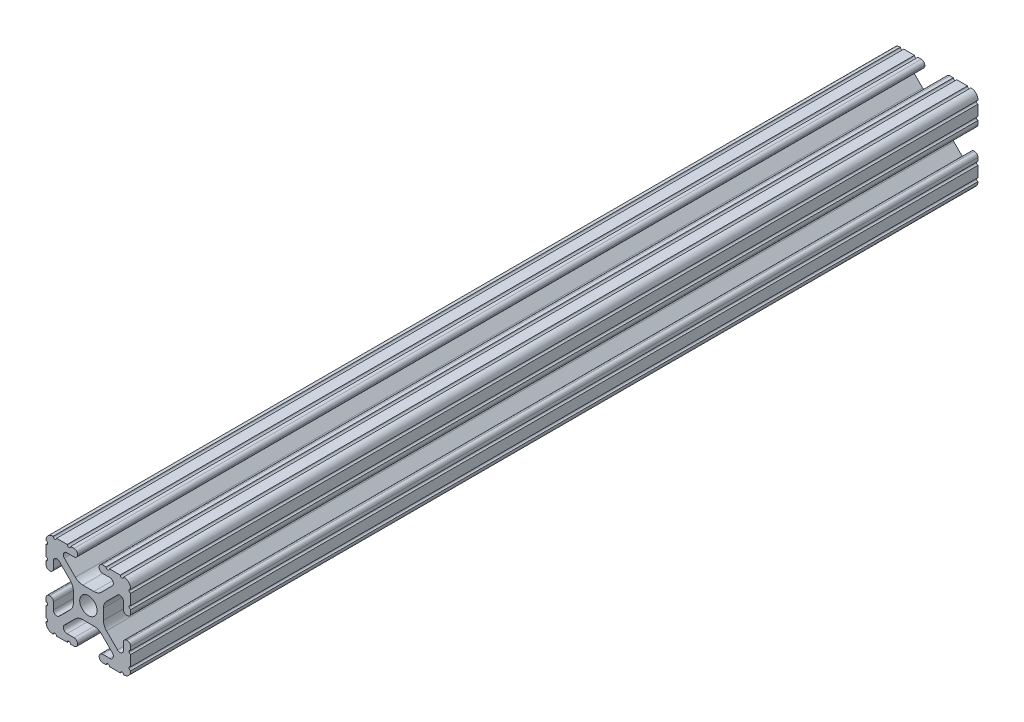
SolidWorks part; units mm, degrees
ref_plane "Front" through (0, 0, 0) normal (0, 0, 1) x (1, 0, 0)
ref_plane "Top" through (0, 0, 0) normal (0, 1, 0) x (1, 0, 0)
ref_plane "Right" through (0, 0, 0) normal (1, 0, 0) x (0, 0, -1)
sketch "Sketch1" plane through (0, 0, 0) normal (0, 0, 1) x (1, 0, 0)
  line L0 (-7.5107, 9.4563) -> (7.5107, 9.4563) construction
  line L1 (-7.4968, -9.4098) -> (7.4968, -9.4098) construction
  line L88 (-7.1797, -8.6452) -> (-3.9523, -5.4237)
  line L89 (-1.7093, -4.4958) -> (1.7093, -4.4958)
  line L90 (3.9523, -5.4237) -> (7.1797, -8.6452)
  line L91 (6.4164, -10.4902) -> (4.2875, -10.4902)
  line L92 (3.2385, -11.5392) -> (3.2385, -11.651)
  line L93 (4.2875, -12.7) -> (5.3171, -12.7)
  line L94 (6.3331, -12.7) -> (9.5504, -12.7)
  line L95 (12.7, -9.5504) -> (12.7, -6.3331)
  line L96 (12.7, -5.3171) -> (12.7, -4.2875)
  line L97 (11.651, -3.2385) -> (11.5392, -3.2385)
  line L98 (10.4902, -4.2875) -> (10.4902, -6.4021)
  line L99 (8.7371, -7.1294) -> (5.441, -3.8408)
  line L100 (4.5085, -1.5932) -> (4.5085, 1.5932)
  line L101 (5.441, 3.8408) -> (8.7371, 7.1294)
  line L102 (10.4902, 6.4021) -> (10.4902, 4.2875)
  line L103 (11.5392, 3.2385) -> (11.651, 3.2385)
  line L104 (12.7, 4.2875) -> (12.7, 5.3171)
  line L105 (12.7, 6.3331) -> (12.7, 9.5504)
  line L106 (9.5504, 12.7) -> (6.3331, 12.7)
  line L107 (5.3171, 12.7) -> (4.2875, 12.7)
  line L108 (3.2385, 11.651) -> (3.2385, 11.5392)
  line L109 (4.2875, 10.4902) -> (6.4768, 10.4902)
  line L110 (7.207, 8.7244) -> (3.8983, 5.4232)
  line L111 (1.6558, 4.4958) -> (-1.6558, 4.4958)
  line L112 (-3.8983, 5.4232) -> (-7.207, 8.7244)
  line L113 (-6.4768, 10.4902) -> (-4.2875, 10.4902)
  line L114 (-3.2385, 11.5392) -> (-3.2385, 11.651)
  line L115 (-4.2875, 12.7) -> (-5.3171, 12.7)
  line L116 (-6.3331, 12.7) -> (-9.5504, 12.7)
  line L117 (-12.7, 9.5504) -> (-12.7, 6.3331)
  line L118 (-12.7, 5.3171) -> (-12.7, 4.2875)
  line L119 (-11.651, 3.2385) -> (-11.5392, 3.2385)
  line L120 (-10.4902, 4.2875) -> (-10.4902, 6.4021)
  line L121 (-8.7371, 7.1294) -> (-5.441, 3.8408)
  line L122 (-4.5085, 1.5932) -> (-4.5085, -1.5932)
  line L123 (-5.441, -3.8408) -> (-8.7371, -7.1294)
  line L124 (-10.4902, -6.4021) -> (-10.4902, -4.2875)
  line L125 (-11.5392, -3.2385) -> (-11.651, -3.2385)
  line L126 (-12.7, -4.2875) -> (-12.7, -5.3171)
  line L127 (-12.7, -6.3331) -> (-12.7, -9.5504)
  line L128 (-9.5504, -12.7) -> (-6.3331, -12.7)
  line L129 (-5.3171, -12.7) -> (-4.2875, -12.7)
  line L130 (-3.2385, -11.651) -> (-3.2385, -11.5392)
  line L131 (-4.2875, -10.4902) -> (-6.4164, -10.4902)
  circle A1 centre (0, 0) radius 2.6035
  arc A104 (-7.1797, -8.6452) -> (-6.4164, -10.4902) centre (-6.4164, -9.4098) ccw
  arc A105 (-1.7093, -4.4958) -> (-3.9523, -5.4237) centre (-1.7093, -7.6708) ccw
  arc A106 (3.9523, -5.4237) -> (1.7093, -4.4958) centre (1.7093, -7.6708) ccw
  arc A107 (6.4164, -10.4902) -> (7.1797, -8.6452) centre (6.4164, -9.4098) ccw
  arc A108 (4.2875, -10.4902) -> (3.2385, -11.5392) centre (4.2875, -11.5392) ccw
  arc A109 (3.2385, -11.651) -> (4.2875, -12.7) centre (4.2875, -11.651) ccw
  arc A110 (6.3331, -12.7) -> (5.3171, -12.7) centre (5.8251, -12.7) ccw
  arc A111 (10.5664, -12.6998) -> (9.5504, -12.7) centre (10.0584, -12.7) ccw
  arc A112 (10.5664, -12.6998) -> (12.6998, -10.5664) centre (10.5918, -10.5918) ccw
  arc A113 (12.7, -9.5504) -> (12.6998, -10.5664) centre (12.7, -10.0584) ccw
  arc A114 (12.7, -5.3171) -> (12.7, -6.3331) centre (12.7, -5.8251) ccw
  arc A115 (12.7, -4.2875) -> (11.651, -3.2385) centre (11.651, -4.2875) ccw
  arc A116 (11.5392, -3.2385) -> (10.4902, -4.2875) centre (11.5392, -4.2875) ccw
  arc A117 (8.7371, -7.1294) -> (10.4902, -6.4021) centre (9.4628, -6.4021) ccw
  arc A118 (4.5085, -1.5932) -> (5.441, -3.8408) centre (7.6835, -1.5932) ccw
  arc A119 (5.441, 3.8408) -> (4.5085, 1.5932) centre (7.6835, 1.5932) ccw
  arc A120 (10.4902, 6.4021) -> (8.7371, 7.1294) centre (9.4628, 6.4021) ccw
  arc A121 (10.4902, 4.2875) -> (11.5392, 3.2385) centre (11.5392, 4.2875) ccw
  arc A122 (11.651, 3.2385) -> (12.7, 4.2875) centre (11.651, 4.2875) ccw
  arc A123 (12.7, 6.3331) -> (12.7, 5.3171) centre (12.7, 5.8251) ccw
  arc A124 (12.6998, 10.5664) -> (12.7, 9.5504) centre (12.7, 10.0584) ccw
  arc A125 (12.6998, 10.5664) -> (10.5664, 12.6998) centre (10.5918, 10.5918) ccw
  arc A126 (9.5504, 12.7) -> (10.5664, 12.6998) centre (10.0584, 12.7) ccw
  arc A127 (5.3171, 12.7) -> (6.3331, 12.7) centre (5.8251, 12.7) ccw
  arc A128 (4.2875, 12.7) -> (3.2385, 11.651) centre (4.2875, 11.651) ccw
  arc A129 (3.2385, 11.5392) -> (4.2875, 10.4902) centre (4.2875, 11.5392) ccw
  arc A130 (7.207, 8.7244) -> (6.4768, 10.4902) centre (6.4768, 9.4563) ccw
  arc A131 (1.6558, 4.4958) -> (3.8983, 5.4232) centre (1.6558, 7.6708) ccw
  arc A132 (-3.8983, 5.4232) -> (-1.6558, 4.4958) centre (-1.6558, 7.6708) ccw
  arc A133 (-6.4768, 10.4902) -> (-7.207, 8.7244) centre (-6.4768, 9.4563) ccw
  arc A134 (-4.2875, 10.4902) -> (-3.2385, 11.5392) centre (-4.2875, 11.5392) ccw
  arc A135 (-3.2385, 11.651) -> (-4.2875, 12.7) centre (-4.2875, 11.651) ccw
  arc A136 (-6.3331, 12.7) -> (-5.3171, 12.7) centre (-5.8251, 12.7) ccw
  arc A137 (-10.5664, 12.6998) -> (-9.5504, 12.7) centre (-10.0584, 12.7) ccw
  arc A138 (-10.5664, 12.6998) -> (-12.6998, 10.5664) centre (-10.5918, 10.5918) ccw
  arc A139 (-12.7, 9.5504) -> (-12.6998, 10.5664) centre (-12.7, 10.0584) ccw
  arc A140 (-12.7, 5.3171) -> (-12.7, 6.3331) centre (-12.7, 5.8251) ccw
  arc A141 (-12.7, 4.2875) -> (-11.651, 3.2385) centre (-11.651, 4.2875) ccw
  arc A142 (-11.5392, 3.2385) -> (-10.4902, 4.2875) centre (-11.5392, 4.2875) ccw
  arc A143 (-8.7371, 7.1294) -> (-10.4902, 6.4021) centre (-9.4628, 6.4021) ccw
  arc A144 (-4.5085, 1.5932) -> (-5.441, 3.8408) centre (-7.6835, 1.5932) ccw
  arc A145 (-5.441, -3.8408) -> (-4.5085, -1.5932) centre (-7.6835, -1.5932) ccw
  arc A146 (-10.4902, -6.4021) -> (-8.7371, -7.1294) centre (-9.4628, -6.4021) ccw
  arc A147 (-10.4902, -4.2875) -> (-11.5392, -3.2385) centre (-11.5392, -4.2875) ccw
  arc A148 (-11.651, -3.2385) -> (-12.7, -4.2875) centre (-11.651, -4.2875) ccw
  arc A149 (-12.7, -6.3331) -> (-12.7, -5.3171) centre (-12.7, -5.8251) ccw
  arc A150 (-12.6998, -10.5664) -> (-12.7, -9.5504) centre (-12.7, -10.0584) ccw
  arc A151 (-12.6998, -10.5664) -> (-10.5664, -12.6998) centre (-10.5918, -10.5918) ccw
  arc A152 (-9.5504, -12.7) -> (-10.5664, -12.6998) centre (-10.0584, -12.7) ccw
  arc A153 (-5.3171, -12.7) -> (-6.3331, -12.7) centre (-5.8251, -12.7) ccw
  arc A154 (-4.2875, -12.7) -> (-3.2385, -11.651) centre (-4.2875, -11.651) ccw
  arc A155 (-3.2385, -11.5392) -> (-4.2875, -10.4902) centre (-4.2875, -11.5392) ccw
extrude "Boss-Extrude1" add sketch "Sketch1" along normal mid plane 254
